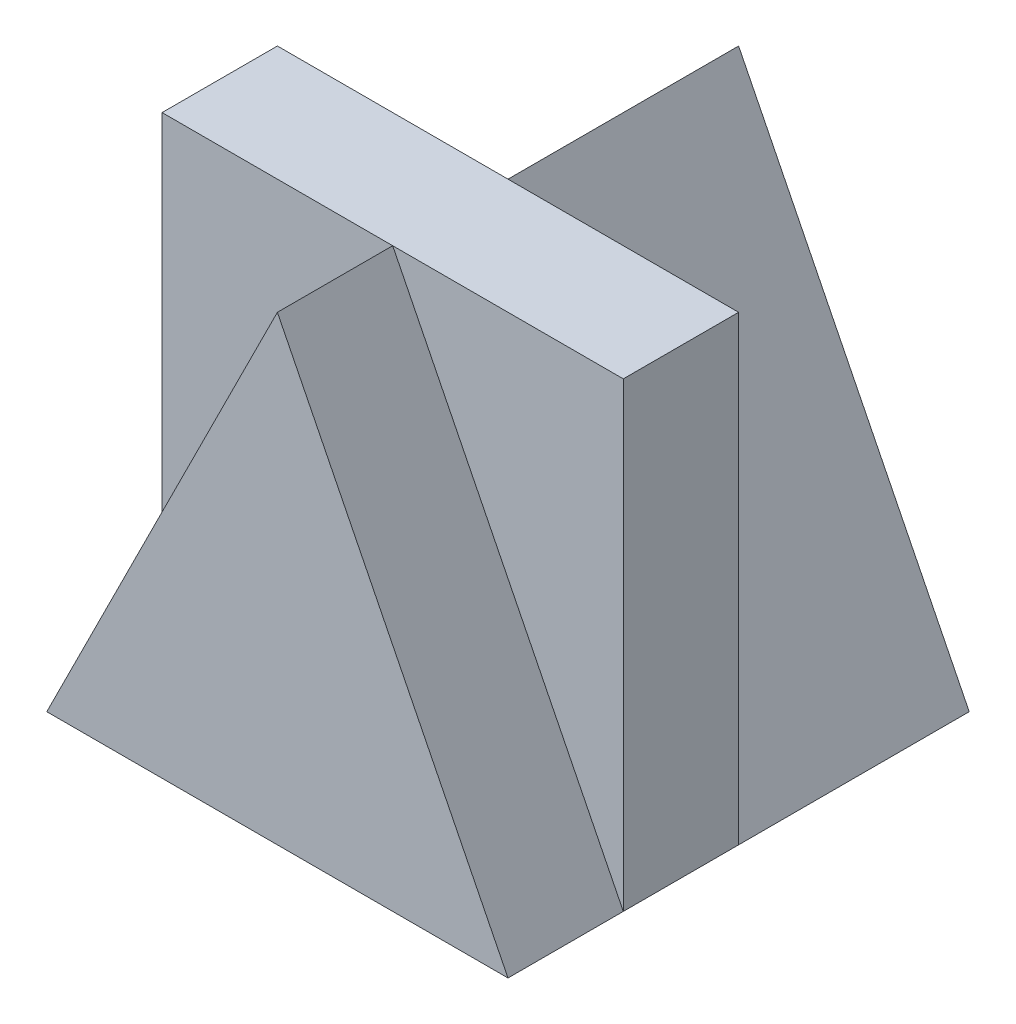
SolidWorks part; units mm, degrees
ref_plane "Front" through (0, 0, 0) normal (0, 0, 1) x (1, 0, 0)
ref_plane "Top" through (0, 0, 0) normal (0, 1, 0) x (1, 0, 0)
ref_plane "Right" through (0, 0, 0) normal (1, 0, 0) x (0, 0, -1)
sketch "Sketch1" plane through (0, 0, 0) normal (0, 1, 0) x (1, 0, 0)
  line L1 (-2, -2) -> (2, -2)
  line L2 (-2, -2) -> (-2, 2)
  line L3 (-2, 2) -> (2, 2)
  line L4 (2, -2) -> (2, 2)
  line L5 (-2, -2) -> (2, 2) construction
  line L6 (-2, 2) -> (2, -2) construction
  point P0 (0, 0)
  dimension "D1" = 4
  dimension "D2" = 4
extrude "Boss-Extrude1" add sketch "Sketch1" along normal blind 4
sketch "Sketch6" plane through (0, 0, 2) normal (0, 0, 1) x (1, 0, 0)
  line L0 (0, 4) -> (-2, 4)
  line L1 (-2, 4) -> (2, 4) construction
  line L2 (-2, 4) -> (-2, 0)
  line L3 (-2, 0) -> (0, 4)
  line L4 (0, 4) -> (2, 0)
  line L5 (2, 0) -> (2, 4)
  line L6 (2, 4) -> (0, 4)
  line M5 (2, 0) -> (2, 4)
  line M6 (2, 4) -> (-2, 4)
  line M7 (-2, 4) -> (-2, 0)
extrude "Cut-Extrude3" cut sketch "Sketch6" against normal blind 1 contours L3 M7 M6 | L4 M6 M5
sketch "Sketch8" plane through (0, 0, -2) normal (0, 0, -1) x (-1, 0, 0)
  line L0 (-2, 0) -> (-2, 4)
  line L1 (-2, 4) -> (2, 4)
  line L2 (2, 4) -> (2, 0)
  line L3 (2, 0) -> (0, 4)
  line L4 (0, 4) -> (-2, 0)
  line M2 (2, 0) -> (2, 4)
  line M3 (2, 4) -> (-2, 4)
  line M4 (-2, 4) -> (-2, 0)
extrude "Cut-Extrude5" cut sketch "Sketch8" against normal blind 2 contours L4 L1 M4 | L3 M2 M3
